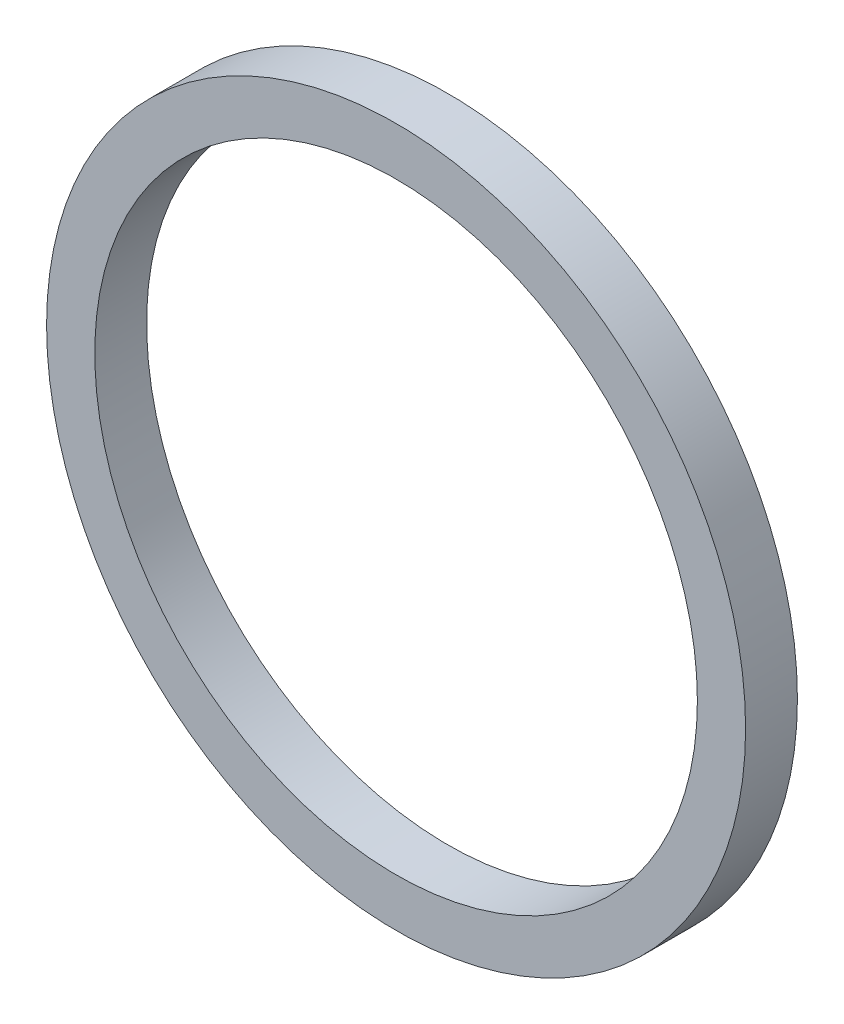
SolidWorks part; units mm, degrees
material "Silicon"
ref_plane "Front" through (0, 0, 0) normal (0, 0, 1) x (1, 0, 0)
ref_plane "Top" through (0, 0, 0) normal (0, 1, 0) x (1, 0, 0)
ref_plane "Right" through (0, 0, 0) normal (1, 0, 0) x (0, 0, -1)
sketch "Sketch1" plane through (0, 0, 0) normal (0, 0, 1) x (1, 0, 0)
  circle A0 centre (0, 0) radius 87
  circle A1 centre (0, 0) radius 75
extrude "Boss-Extrude1" add sketch "Sketch1" along normal blind 12.9
